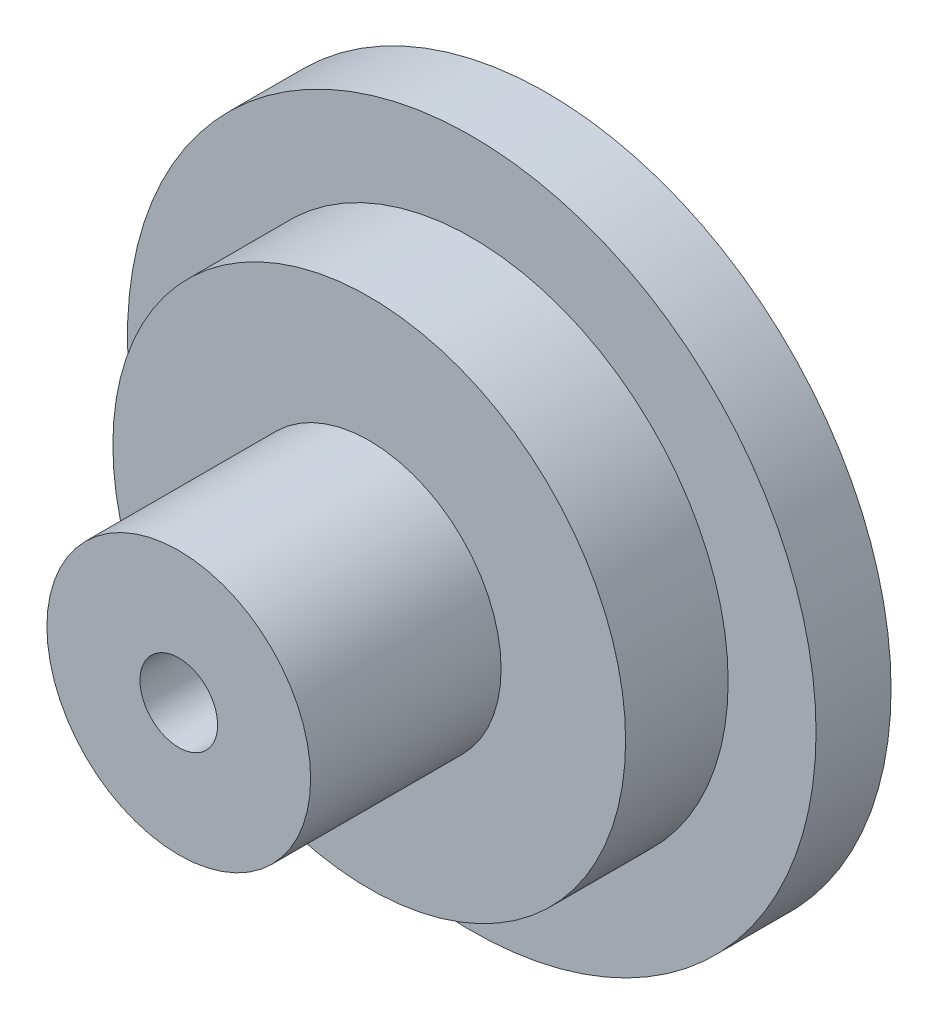
SolidWorks part; units mm, degrees
ref_plane "Front Plane" through (0, 0, 0) normal (0, 0, 1) x (1, 0, 0)
ref_plane "Top Plane" through (0, 0, 0) normal (0, 1, 0) x (1, 0, 0)
ref_plane "Right Plane" through (0, 0, 0) normal (1, 0, 0) x (0, 0, -1)
sketch "Sketch1" plane through (0, 0, 0) normal (0, 0, 1) x (1, 0, 0)
  circle A0 centre (0, 0) radius 23.5
  dimension "D1" = 47
extrude "Boss-Extrude1" add sketch "Sketch1" along normal blind 5.12
sketch "Sketch2" plane through (0, 0, 5.12) normal (0, 0, 1) x (1, 0, 0)
  circle A0 centre (0, 0) radius 17.5
  dimension "D1" = 35
extrude "Boss-Extrude2" add sketch "Sketch2" along normal blind 7
sketch "Sketch3" plane through (0, 0, 12.12) normal (0, 0, 1) x (1, 0, 0)
  circle A0 centre (0, 0) radius 9
  dimension "D1" = 18
extrude "Boss-Extrude3" add sketch "Sketch3" along normal blind 13
hole_wizard "CSK for M5 SFHCS1" positions "Sketch5" profile "Sketch6" countersink size "M5" standard "ANSI Metric" end condition through all
sketch "Sketch5" plane through (0, 0, 0) normal (0, 0, -1) x (-1, 0, 0)
  point P0 (0, 0)
sketch "Sketch6" plane through (0, 0, 0) normal (1, 0, 0) x (0, 1, 0)
  line L0 (0, 0) -> (0, 25.12)
  line L1 (0, 25.12) -> (2.65, 25.12)
  line L2 (2.65, 25.12) -> (2.65, 2.95)
  line L3 (2.65, 2.95) -> (5.6, 0)
  line L5 (5.6, 0) -> (0, 0)
  line L6 (-2.65, 2.95) -> (-5.6, 0) construction
  line L11 (0, -6.35) -> (0, 107.95) construction
  dimension "Thru Hole Dia." = 5.3
  dimension "Thru Hole Depth" = 25.12
  dimension "Near C'Sink Dia." = 11.2
  dimension "Near C'Sink Angle" = 90
